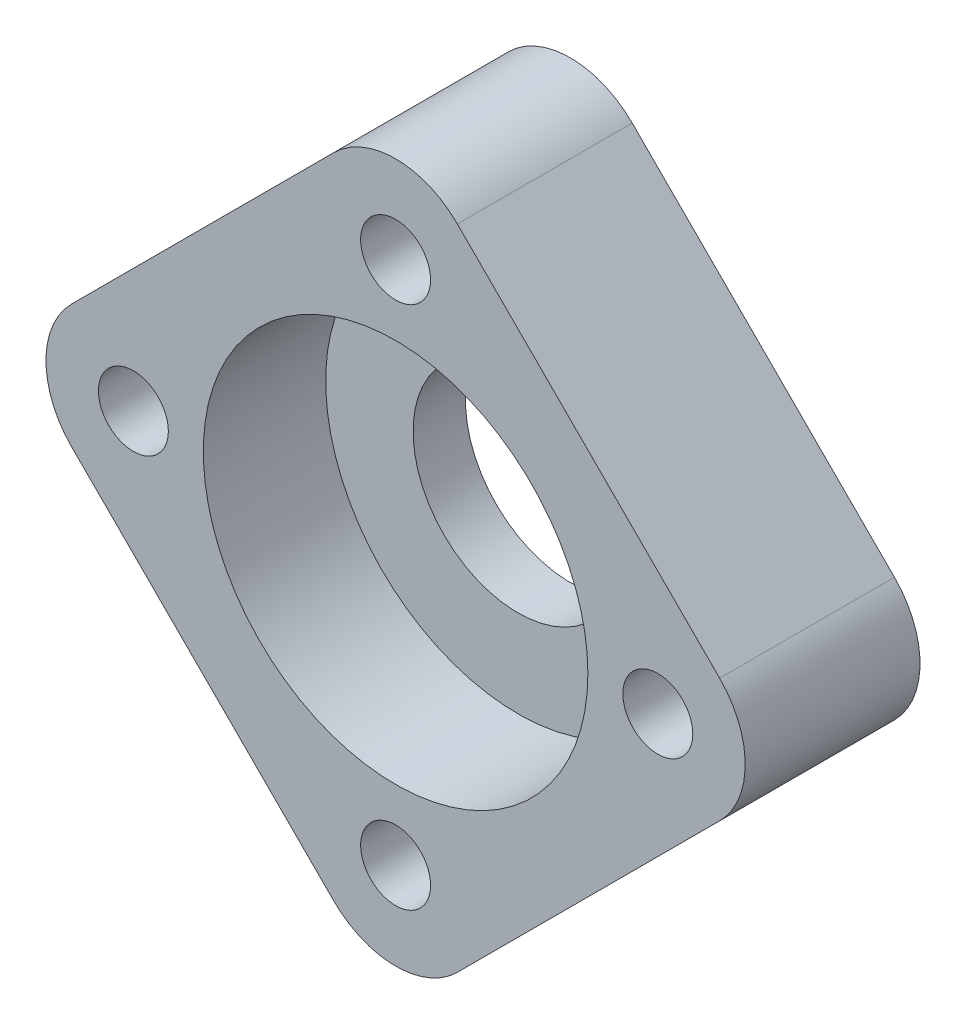
SolidWorks part; units mm, degrees
material "PET"
ref_plane "Front Plane" through (0, 0, 0) normal (0, 0, 1) x (1, 0, 0)
ref_plane "Top Plane" through (0, 0, 0) normal (0, 1, 0) x (1, 0, 0)
ref_plane "Right Plane" through (0, 0, 0) normal (1, 0, 0) x (0, 0, -1)
sketch "Sketch1" plane through (0, 0, 0) normal (0, 0, 1) x (1, 0, 0)
  line L0 (-18.5355, 3.5355) -> (-3.5355, 18.5355)
  line L1 (3.5355, 18.5355) -> (18.5355, 3.5355)
  line L2 (18.5355, -3.5355) -> (3.5355, -18.5355)
  line L3 (-3.5355, -18.5355) -> (-18.5355, -3.5355)
  circle A0 centre (0, 0) radius 15 construction
  circle A1 centre (0, 15) radius 2
  circle A2 centre (15, 0) radius 2
  circle A3 centre (0, -15) radius 2
  circle A4 centre (-15, 0) radius 2
  arc A5 (3.5355, 18.5355) -> (-3.5355, 18.5355) centre (0, 15) ccw
  arc A7 (-3.5355, -18.5355) -> (3.5355, -18.5355) centre (0, -15) ccw
  arc A8 (-18.5355, 3.5355) -> (-18.5355, -3.5355) centre (-15, 0) ccw
  arc A9 (18.5355, -3.5355) -> (18.5355, 3.5355) centre (15, 0) ccw
  arc A10 (14.1667, 4.9301) -> (14.1667, -4.9301) centre (15, 0) ccw [skipped]
  point P14 (0, 0)
  point P21 (0, 0)
  dimension "D1" = 4
  dimension "D2" = 30
  dimension "D4" = 10
  dimension "D3" = 4
  dimension "D5" = 4
extrude "Boss-Extrude1" add sketch "Sketch1" along normal blind 10
sketch "Sketch2" plane through (0, 0, 10) normal (0, 0, 1) x (1, 0, 0)
  circle A0 centre (0, 0) radius 11
  dimension "D1" = 22
extrude "Cut-Extrude1" cut sketch "Sketch2" against normal blind 7
sketch "Sketch3" plane through (0, 0, 3) normal (0, 0, 1) x (1, 0, 0)
  circle A0 centre (0, 0) radius 6
  dimension "D1" = 12
extrude "Cut-Extrude2" cut sketch "Sketch3" against normal blind 7
